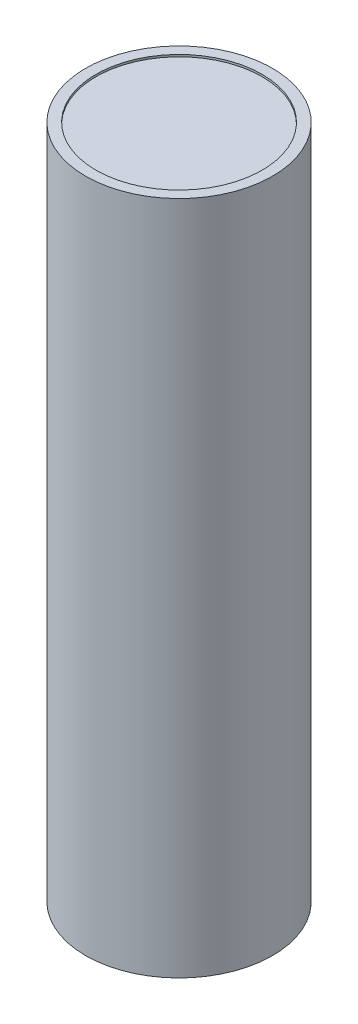
SolidWorks part; units mm, degrees
ref_plane "Front Plane" through (0, 0, 0) normal (0, 0, 1) x (1, 0, 0)
ref_plane "Top Plane" through (0, 0, 0) normal (0, 1, 0) x (1, 0, 0)
ref_plane "Right Plane" through (0, 0, 0) normal (1, 0, 0) x (0, 0, -1)
sketch "Sketch1" plane through (0, 0, 0) normal (0, 1, 0) x (1, 0, 0)
  circle A0 centre (0, 0) radius 9
  dimension "D1" = 18
extrude "Boss-Extrude1" add sketch "Sketch1" along normal blind 65
sketch "Sketch2" plane through (0, 65, 0) normal (0, 1, 0) x (1, 0, 0)
  circle A2 centre (0, 0) radius 8
  circle A3 centre (0, 0) radius 8
  dimension "D1" = 1
extrude "Cut-Extrude1" cut sketch "Sketch2" against normal blind 0.2
sketch "Sketch3" plane through (0, 0, 0) normal (0, -1, 0) x (1, 0, 0)
  circle A2 centre (0, 0) radius 8
  circle A3 centre (0, 0) radius 8
  dimension "D1" = 1
extrude "Cut-Extrude2" cut sketch "Sketch3" against normal blind 0.2
